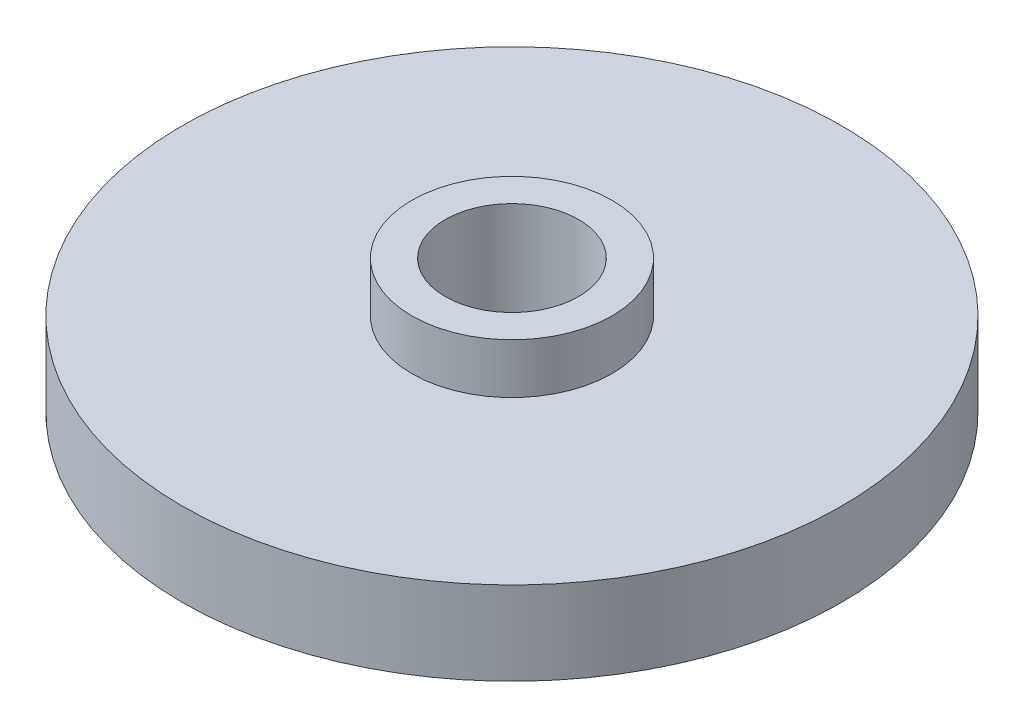
SolidWorks part; units mm, degrees
ref_plane "Front Plane" through (0, 0, 0) normal (0, 0, 1) x (1, 0, 0)
ref_plane "Top Plane" through (0, 0, 0) normal (0, 1, 0) x (1, 0, 0)
ref_plane "Right Plane" through (0, 0, 0) normal (1, 0, 0) x (0, 0, -1)
sketch "草圖1" plane through (0, 0, 0) normal (0, 1, 0) x (1, 0, 0)
  circle A0 centre (0, 0) radius 19.75
  dimension "D1" = 39.5
extrude "填料-伸長1" add sketch "草圖1" along normal blind 5
sketch "草圖2" plane through (0, 5, 0) normal (0, 1, 0) x (1, 0, 0)
  circle A0 centre (0, 0) radius 6
  dimension "D1" = 12
extrude "填料-伸長2" add sketch "草圖2" along normal blind 3
sketch "草圖3" plane through (0, 0, 0) normal (0, -1, 0) x (1, 0, 0)
  circle A0 centre (0, 0) radius 4.7
  dimension "D1" = 9.4
extrude "填料-伸長3" add sketch "草圖3" along normal blind 0.65
sketch "草圖4" plane through (0, -0.65, 0) normal (0, -1, 0) x (1, 0, 0)
  circle A0 centre (0, 0) radius 1.6
  dimension "D1" = 3.2
extrude "除料-伸長1" cut sketch "草圖4" against normal through all
sketch "草圖5" plane through (0, -0.65, 0) normal (0, -1, 0) x (1, 0, 0)
  circle A0 centre (0, 0) radius 3.85
  circle A1 centre (0, 0) radius 4.7 construction
  dimension "D1" = 0.85
extrude "除料-伸長2" cut sketch "草圖5" against normal blind 0.85
sketch "草圖6" plane through (0, 8, 0) normal (0, 1, 0) x (1, 0, 0)
  circle A0 centre (0, 0) radius 4
  dimension "D1" = 8
extrude "除料-伸長3" cut sketch "草圖6" against normal blind 5.8
